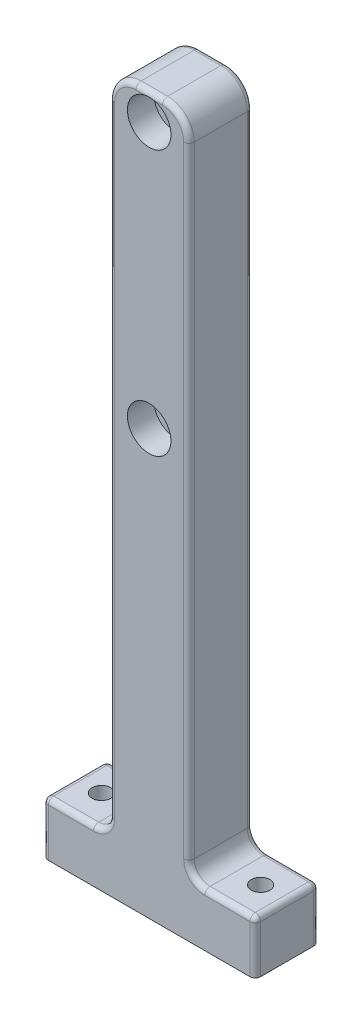
SolidWorks part; units mm, degrees
ref_plane "正面" through (0, 0, 0) normal (0, 0, 1) x (1, 0, 0)
ref_plane "平面" through (0, 0, 0) normal (0, 1, 0) x (1, 0, 0)
ref_plane "右側面" through (0, 0, 0) normal (1, 0, 0) x (0, 0, -1)
sketch "ｽｹｯﾁ1" plane through (0, 0, 0) normal (0, 0, 1) x (1, 0, 0)
  line L1 (7.5, -67.5) -> (-7.5, -67.5)
  line L2 (7.5, -67.5) -> (7.5, 67.5)
  line L3 (7.5, 67.5) -> (-7.5, 67.5)
  line L4 (-7.5, -67.5) -> (-7.5, 67.5)
  line L5 (7.5, -67.5) -> (-7.5, 67.5) construction
  line L6 (7.5, 67.5) -> (-7.5, -67.5) construction
  line L7 (-20, -57.5) -> (20, -57.5)
  line L8 (-20, -57.5) -> (-20, -67.5)
  line L9 (-20, -67.5) -> (20, -67.5)
  line L10 (20, -57.5) -> (20, -67.5)
  line L11 (-20, -57.5) -> (20, -67.5) construction
  line L12 (-20, -67.5) -> (20, -57.5) construction
  point P0 (0, 0)
  point P6 (0, -62.5)
  dimension "D1" = 15
  dimension "D2" = 135
  dimension "D3" = 10
  dimension "D4" = 40
  dimension "D5" = 0
  dimension "D6" = 0
extrude "ﾎﾞｽ - 押し出し1" add sketch "ｽｹｯﾁ1" along normal blind 12 contours L2 L3 L4 L1 | L7 L10 L9 L8
sketch "ｽｹｯﾁ2" plane through (0, 0, 12) normal (0, 0, 1) x (1, 0, 0)
  line L0 (20, -67.5) -> (-20, -67.5) construction
  circle A0 centre (0, 12.5) radius 4.1
  circle A1 centre (0, 62.5) radius 4.1
  dimension "D1" = 8.2
  dimension "D3" = 50
  dimension "D4" = 8.2
  dimension "D2" = 80
sketch "ｽｹｯﾁ3" plane through (0, -57.5, 0) normal (0, 1, 0) x (1, 0, 0)
  line L0 (20, -12) -> (20, 0) construction
  line L1 (-20, -12) -> (-20, 0) construction
  line L2 (7.5, 0) -> (20, 0) construction
  line L3 (-20, 0) -> (-7.5, 0) construction
  circle A0 centre (-15, -6) radius 1.75
  circle A1 centre (15, -6) radius 1.75
  dimension "D1" = 3.5
  dimension "D2" = 3.5
  dimension "D4" = 5
  dimension "D5" = 6
  dimension "D6" = 6
  dimension "D3" = 5
extrude "ｶｯﾄ - 押し出し1" cut sketch "ｽｹｯﾁ3" against normal through all
fillet "ﾌｨﾚｯﾄ1" radius 3 2 edges at (7.5, -57.5, 6) (-7.5, -57.5, 6)
fillet "ﾌｨﾚｯﾄ2" radius 5 2 edges at (7.5, 67.5, 6) (-7.5, 67.5, 6)
fillet "ﾌｨﾚｯﾄ3" radius 1 24 edges at (15.25, -57.5, 12) (8.3787, -56.6213, 12) (7.5, 4, 12) (6.0355, 66.0355, 12) (0, 67.5, 12) (-6.0355, 66.0355, 12) (-7.5, 4, 12) (-8.3787, -56.6213, 12) (15.25, -57.5, 0) (8.3787, -56.6213, 0) (7.5, 4, 0) (6.0355, 66.0355, 0) (0, 67.5, 0) (-6.0355, 66.0355, 0) (-7.5, 4, 0) (-8.3787, -56.6213, 0) (20, -62.5, 12) (20, -62.5, 0) (20, -57.5, 6) (-15.25, -57.5, 12) (-20, -62.5, 12) (-20, -62.5, 0) (-15.25, -57.5, 0) (-20, -57.5, 6)
extrude "ｶｯﾄ - 押し出し2" cut sketch "ｽｹｯﾁ2" against normal blind 5
